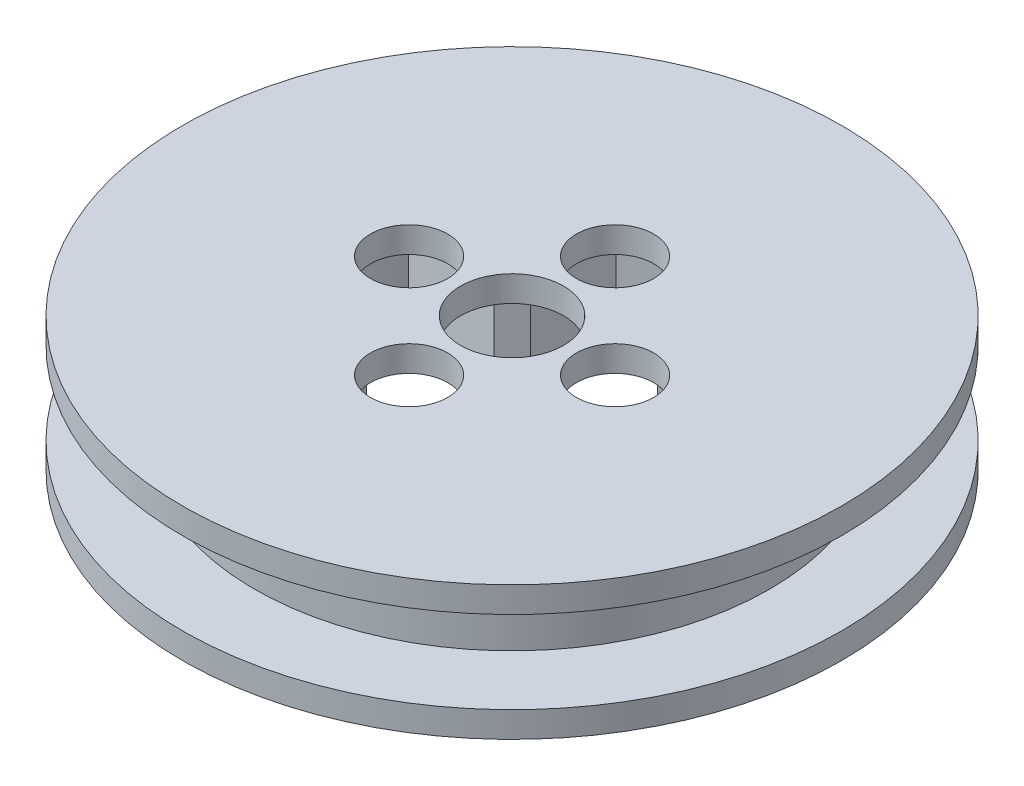
SolidWorks part; units mm, degrees
ref_plane "Front Plane" through (0, 0, 0) normal (0, 0, 1) x (1, 0, 0)
ref_plane "Top Plane" through (0, 0, 0) normal (0, 1, 0) x (1, 0, 0)
ref_plane "Right Plane" through (0, 0, 0) normal (1, 0, 0) x (0, 0, -1)
sketch "Sketch1" plane through (0, -4.6409, 0) normal (0, -1, 0) x (1, 0, 0)
  line L0 (58.4526, 12.4469) -> (71.1526, 12.4469) construction
  line L1 (64.8026, 18.7969) -> (64.8026, 6.0969) construction
  circle A8 centre (64.8026, 12.4469) radius 20.32
  circle A9 centre (64.8026, 12.4469) radius 3.175
  circle A10 centre (58.4526, 12.4469) radius 2.3812
  circle A11 centre (71.1526, 12.4469) radius 2.3813
  circle A12 centre (64.8026, 18.7969) radius 2.3813
  circle A13 centre (64.8026, 6.0969) radius 2.3813
  point P2 (64.8026, 12.4469)
  point P7 (64.8026, 12.4469)
  dimension "D1" = 40.64
  dimension "D2" = 6.35
  dimension "D4" = 4.7625
  dimension "D3" = 12.7
extrude "Boss-Extrude1" add sketch "Sketch1" along normal blind 1.5875
sketch "Sketch2" plane through (0, -6.2284, 0) normal (0, -1, 0) x (1, 0, 0)
  circle A0 centre (64.8026, 12.4469) radius 15.875
  circle A6 centre (64.8026, 12.4469) radius 13.589
  dimension "D1" = 31.75
  dimension "D3" = 2.286
extrude "Boss-Extrude2" add sketch "Sketch2" along normal blind 5.08
sketch "Sketch3" plane through (0, -11.3084, 0) normal (0, -1, 0) x (1, 0, 0)
  circle A0 centre (64.8026, 12.4469) radius 20.32 construction
  circle A1 centre (64.8026, 12.4469) radius 20.32
  circle A2 centre (64.8026, 12.4469) radius 13.589 construction
  circle A3 centre (64.8026, 12.4469) radius 13.589
extrude "Boss-Extrude3" add sketch "Sketch3" along normal blind 1.5875
sketch "Sketch4" plane through (0, -6.2284, 0) normal (0, -1, 0) x (1, 0, 0)
  line L0 (52.5422, 18.3074) -> (59.7512, 16.3758)
  line L1 (59.7512, 16.3758) -> (60.8737, 17.4983)
  line L2 (60.8737, 17.4983) -> (58.9421, 24.7072)
  line L3 (64.8026, 12.4469) -> (55.1937, 22.0558) construction
  line L4 (51.2136, 12.4469) -> (64.8026, 12.4469) construction
  line L5 (70.6631, 24.7072) -> (68.7314, 17.4983)
  line L6 (69.854, 16.3758) -> (77.0629, 18.3074)
  line L7 (64.8026, 12.4469) -> (74.4114, 22.0558) construction
  line L8 (68.7314, 17.4983) -> (69.854, 16.3758)
  line L9 (77.0629, 6.5864) -> (69.854, 8.518)
  line L10 (68.7314, 7.3955) -> (70.6631, 0.1866)
  line L11 (64.8026, 12.4469) -> (74.4114, 2.838) construction
  line L12 (69.854, 8.518) -> (68.7314, 7.3955)
  line L13 (58.9421, 0.1866) -> (60.8737, 7.3955)
  line L14 (59.7512, 8.518) -> (52.5422, 6.5864)
  line L15 (64.8026, 12.4469) -> (55.1937, 2.838) construction
  line L16 (60.8737, 7.3955) -> (59.7512, 8.518)
  arc A0 (77.0629, 18.3074) -> (70.6631, 24.7072) centre (64.8026, 12.4469) ccw
  circle A1 centre (64.8026, 12.4469) radius 13.589
  arc A2 (58.9421, 24.7072) -> (52.5422, 18.3074) centre (64.8026, 12.4469) ccw
  arc A3 (70.6631, 0.1866) -> (77.0629, 6.5864) centre (64.8026, 12.4469) ccw
  arc A4 (52.5422, 6.5864) -> (58.9421, 0.1866) centre (64.8026, 12.4469) ccw
  circle A5 centre (64.8026, 12.4469) radius 13.589 construction
  circle A6 centre (64.8026, 12.4469) radius 13.589 construction
  point P9 (60.3124, 16.937)
  point P28 (64.8026, 12.4469)
  dimension "D2" = 45
  dimension "D3" = 6.35
  dimension "D4" = 120
  dimension "D5" = 1.5875
  dimension "D1" = 0
  dimension "D6" = 4
extrude "Boss-Extrude4" add sketch "Sketch4" along normal up to surface (6.6675 mm away) up to face at (85.1226, -12.8959, 12.4469)
